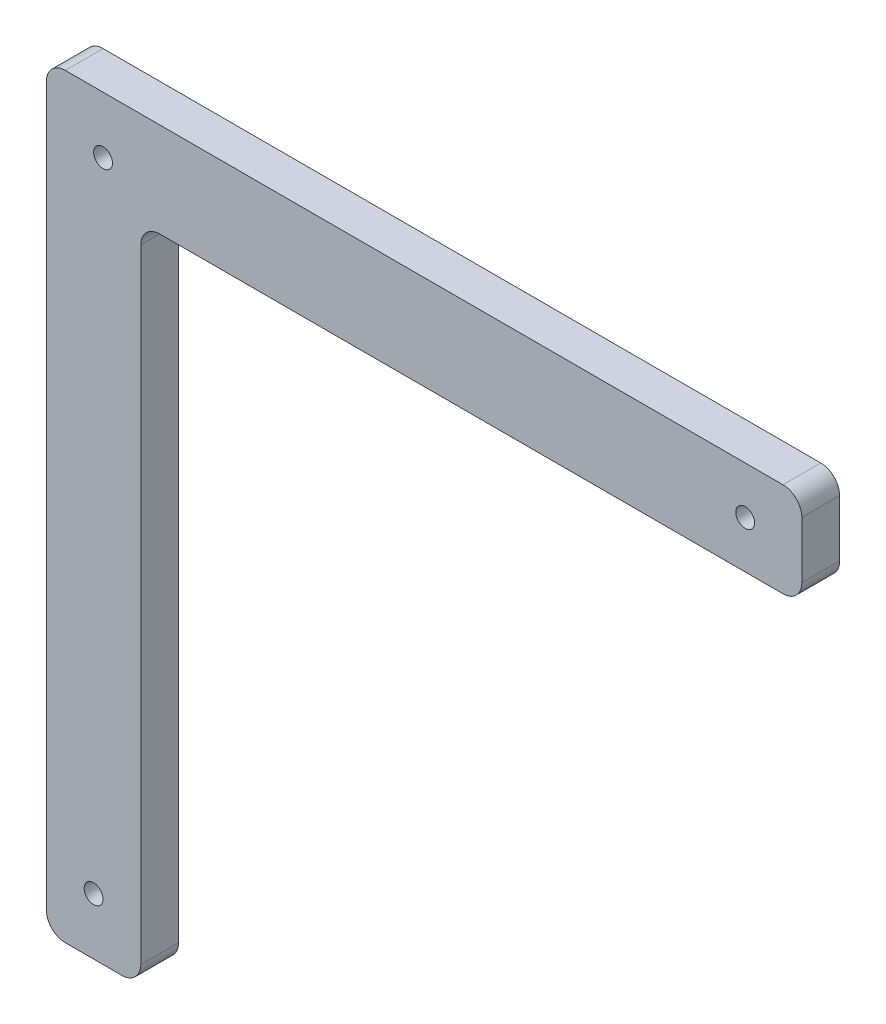
SolidWorks part; units mm, degrees
ref_plane "Front Plane" through (0, 0, 0) normal (0, 0, 1) x (1, 0, 0)
ref_plane "Top Plane" through (0, 0, 0) normal (0, 1, 0) x (1, 0, 0)
ref_plane "Right Plane" through (0, 0, 0) normal (1, 0, 0) x (0, 0, -1)
sketch "Sketch1" plane through (0, 0, 0) normal (0, 0, 1) x (1, 0, 0)
  line L1 (0, 0) -> (400, 0)
  line L2 (0, 0) -> (0, 400)
  line L3 (0, 400) -> (400, 400)
  line L4 (400, 0) -> (400, 400)
  line L5 (0, 0) -> (50, 0)
  line L6 (0, 0) -> (0, 400)
  line L7 (0, 400) -> (50, 400)
  line L8 (50, 0) -> (50, 400)
  line L9 (0, 400) -> (400, 400)
  line L10 (0, 400) -> (0, 350)
  line L11 (0, 350) -> (400, 350)
  line L12 (400, 400) -> (400, 350)
  dimension "D1" = 400
  dimension "D2" = 400
  dimension "D3" = 50
  dimension "D4" = 50
extrude "Boss-Extrude1" add sketch "Sketch1" along normal blind 20 contours L11 L2 L1 L8 | L6 L11 L8 L3 | L8 L11 L4 L3
fillet "Fillet1" radius 10 6 edges at (0, 400, 10) (400, 400, 10) (400, 350, 10) (50, 350, 10) (50, 0, 10) (0, 0, 10)
sketch "Sketch2" plane through (0, 0, 20) normal (0, 0, 1) x (1, 0, 0)
  line L0 (10, 0) -> (40, 0) construction
  line L1 (0, 10) -> (0, 390) construction
  line L2 (10, 400) -> (390, 400) construction
  line L3 (400, 360) -> (400, 390) construction
  line L4 (10, 400) -> (390, 400) construction
  line L5 (0, 10) -> (0, 390) construction
  circle A0 centre (25, 30) radius 5
  circle A1 centre (30, 370) radius 5
  circle A2 centre (370, 375) radius 5
  dimension "D1" = 10
  dimension "D3" = 10
  dimension "D6" = 10
  dimension "D2" = 30
  dimension "D4" = 30
  dimension "D5" = 30
  dimension "D7" = 30
  dimension "D8" = 25
  dimension "D9" = 25
extrude "Cut-Extrude1" cut sketch "Sketch2" against normal blind 20
